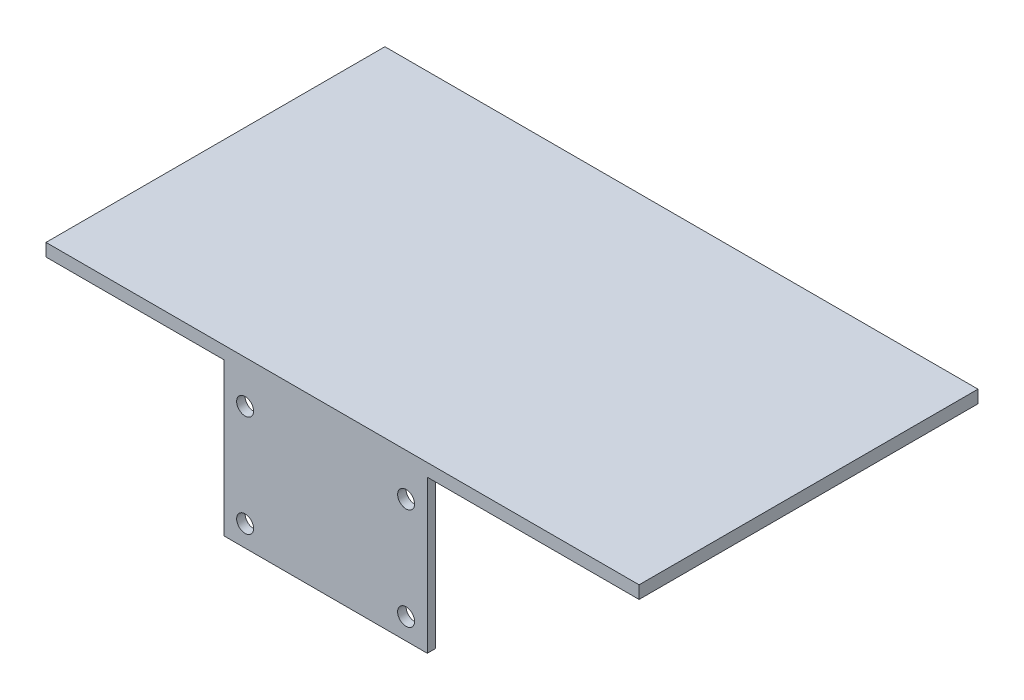
SolidWorks part; units mm, degrees
ref_plane "Front Plane" through (0, 0, 0) normal (0, 0, 1) x (1, 0, 0)
ref_plane "Top Plane" through (0, 0, 0) normal (0, 1, 0) x (1, 0, 0)
ref_plane "Right Plane" through (0, 0, 0) normal (1, 0, 0) x (0, 0, -1)
sketch "Sketch1" plane through (0, 0, 0) normal (0, 0, 1) x (1, 0, 0)
  line L1 (-24, 18) -> (24, 18)
  line L2 (-24, 18) -> (-24, -18)
  line L3 (-24, -18) -> (24, -18)
  line L4 (24, 18) -> (24, -18)
  line L5 (-24, 18) -> (24, -18) construction
  line L6 (-24, -18) -> (24, 18) construction
  line L8 (0, 0) -> (0, 18) construction
  circle A0 centre (-19, 11) radius 2
  circle A3 centre (-19, -13) radius 2
  circle A6 centre (19, -13) radius 2
  circle A7 centre (19, 11) radius 2
  point P0 (0, 0)
  dimension "D3" = 4
  dimension "D4" = 5
  dimension "D5" = 7
  dimension "D6" = 4
  dimension "D7" = 5
  dimension "D8" = 5
  dimension "D1" = 36
  dimension "D2" = 48
extrude "Boss-Extrude1" add sketch "Sketch1" along normal blind 2
sketch "Sketch2" plane through (0, 18, 0) normal (0, 1, 0) x (1, 0, 0)
  line L0 (-66, -2) -> (74, -2)
  line L7 (24, 0) -> (-24, 0) construction
  line L8 (-66, -2) -> (-66, 78)
  line L9 (-66, 78) -> (74, 78)
  line L10 (74, 78) -> (74, -2)
  point P8 (0, 0)
  dimension "D1" = 140
  dimension "D2" = 2
  dimension "D3" = 80
  dimension "D4" = 50
extrude "Boss-Extrude2" add sketch "Sketch2" along normal blind 3
